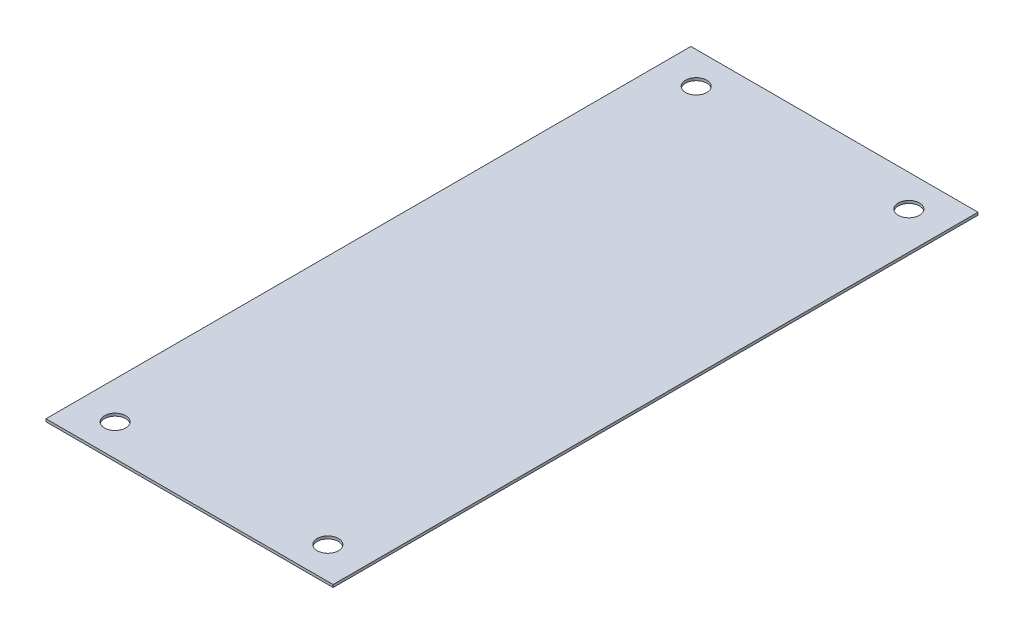
SolidWorks part; units mm, degrees
ref_plane "Front Plane" through (0, 0, 0) normal (0, 0, 1) x (1, 0, 0)
ref_plane "Top Plane" through (0, 0, 0) normal (0, 1, 0) x (1, 0, 0)
ref_plane "Right Plane" through (0, 0, 0) normal (1, 0, 0) x (0, 0, -1)
sketch "Sketch1" plane through (0, 0, 0) normal (0, 1, 0) x (1, 0, 0)
  line L1 (0, 0) -> (342.9, 0)
  line L2 (0, 0) -> (0, 770.128)
  line L3 (0, 770.128) -> (342.9, 770.128)
  line L4 (342.9, 0) -> (342.9, 770.128)
  dimension "D1" = 770.128
  dimension "D2" = 342.9
extrude "Boss-Extrude1" add sketch "Sketch1" along normal blind 3.175
hole_wizard "1 (1) Diameter Hole1" positions "Sketch3" profile "Sketch2" hole size "1" standard "Ansi Inch"
sketch "Sketch3" plane through (0, 3.175, 0) normal (0, 1, 0) x (-1, 0, 0)
  line L0 (0, 0) -> (-342.9, 0) construction
  line L1 (0, -385.064) -> (-342.9, -385.064) construction
  line L2 (0, -770.128) -> (0, 0) construction
  line L3 (-342.9, 0) -> (-342.9, -770.128) construction
  line L4 (-171.45, 0) -> (-171.45, -770.128) construction
  line L5 (-342.9, -770.128) -> (0, -770.128) construction
  line L6 (0, -770.128) -> (0, 0) construction
  point P0 (-44.45, -38.1)
  point P21 (-44.45, -732.028)
  point P23 (-298.45, -732.028)
  point P24 (-298.45, -38.1)
  dimension "D1" = 38.1
  dimension "D2" = 44.45
sketch "Sketch2" plane through (44.45, 3.175, -38.1) normal (1, 0, 0) x (0, 0, 1)
  line L0 (0, 0) -> (0, 28.2049)
  line L1 (0, 28.2049) -> (12.7, 20.574)
  line L2 (12.7, 20.574) -> (12.7, 0)
  line L5 (12.7, 0) -> (0, 0)
  line L10 (0, 28.2049) -> (-12.7, 20.574) construction
  line L11 (0, -6.35) -> (0, 107.95) construction
  dimension "Hole Dia." = 25.4
  dimension "Hole Depth" = 20.574
  dimension "Drill Angle" = 118
